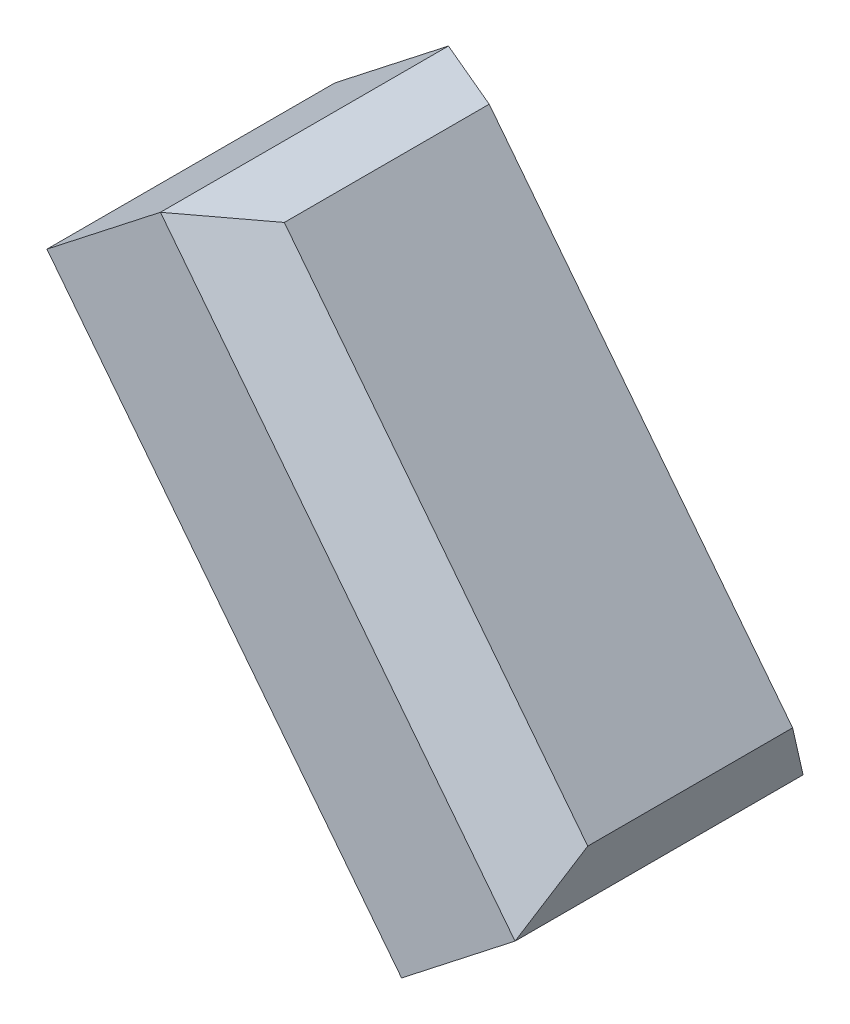
SolidWorks part; units mm, degrees
ref_plane "Front Plane" through (0, 0, 0) normal (0, 0, 1) x (1, 0, 0)
ref_plane "Top Plane" through (0, 0, 0) normal (0, 1, 0) x (1, 0, 0)
ref_plane "Right Plane" through (0, 0, 0) normal (1, 0, 0) x (0, 0, -1)
sketch "Sketch1" plane through (0, 0, 0) normal (0, 1, 0) x (1, 0, 0)
  line L0 (0, -36.1413) -> (0, 60.7695) construction
ref_plane "Plane1" through (0, 0, 0) normal (0.788, 0.6157, 0) x (0, 0, -1)
sketch "Sketch2" plane through (0, 0, 0) normal (0.788, 0.6157, 0) x (0, 0, -1)
  line L1 (0, 0) -> (40, 0)
  line L2 (0, 0) -> (0, 80)
  line L3 (0, 80) -> (40, 80)
  line L4 (40, 0) -> (40, 80)
  dimension "D1" = 80
  dimension "D2" = 40
extrude "Boss-Extrude1" add sketch "Sketch2" along normal blind 30
chamfer "Chamfer1" distance 10 angle 30 4 edges at (-25.6126, 81.5107, -20) (-0.9861, 49.9903, -40) (23.6403, 18.4698, -20) (-0.9861, 49.9903, 0)
